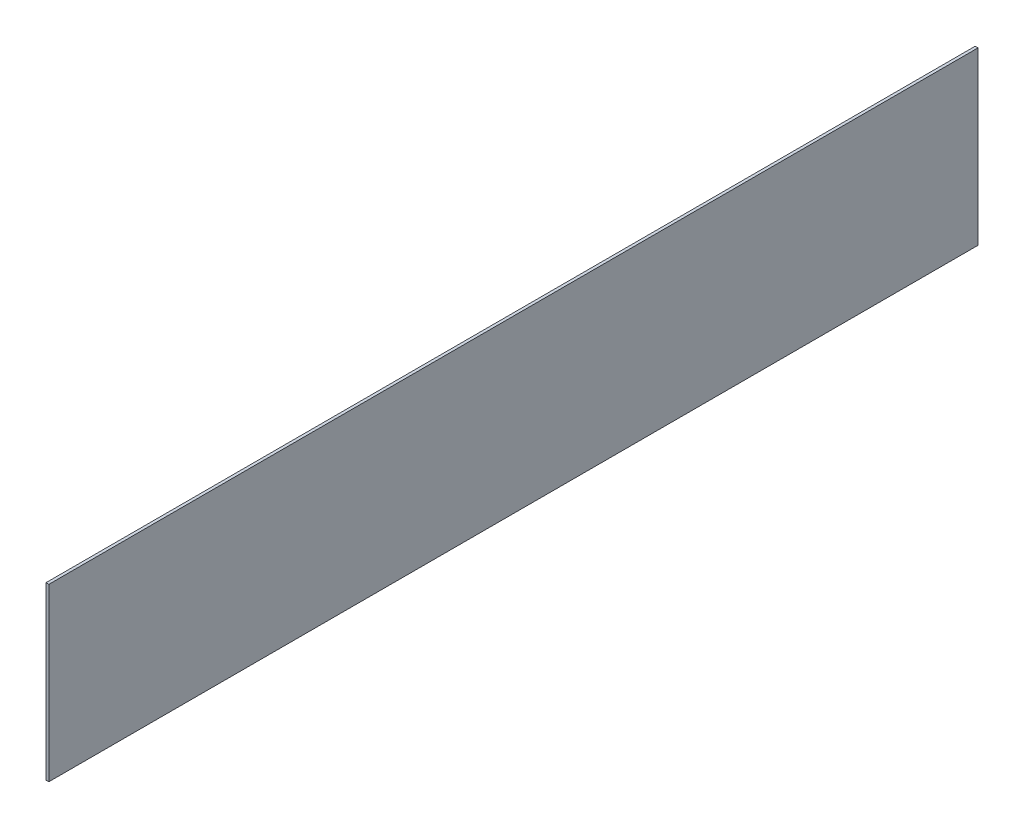
SolidWorks part; units mm, degrees
ref_plane "Front Plane" through (0, 0, 0) normal (0, 0, 1) x (1, 0, 0)
ref_plane "Top Plane" through (0, 0, 0) normal (0, 1, 0) x (1, 0, 0)
ref_plane "Right Plane" through (0, 0, 0) normal (1, 0, 0) x (0, 0, -1)
sketch "Sketch1" plane through (0, 0, 0) normal (1, 0, 0) x (0, 0, -1)
  line L0 (0, 0) -> (0, 60)
  line L1 (0, 60) -> (326, 60)
  line L2 (326, 60) -> (326, 0)
  line L3 (326, 0) -> (0, 0)
  dimension "D1" = 60
  dimension "D2" = 326
extrude "Boss-Extrude1" add sketch "Sketch1" along normal blind 1
